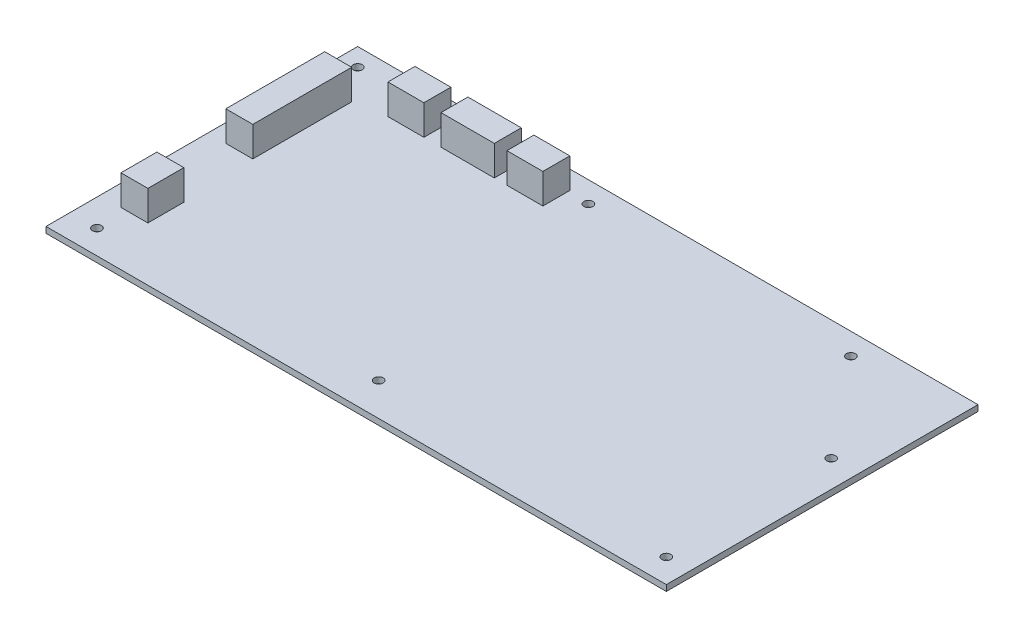
SolidWorks part; units mm, degrees
material "Cuivre"
ref_plane "Plan de face" through (0, 0, 0) normal (0, 0, 1) x (1, 0, 0)
ref_plane "Plan de dessus" through (0, 0, 0) normal (0, 1, 0) x (1, 0, 0)
ref_plane "Plan de droite" through (0, 0, 0) normal (1, 0, 0) x (0, 0, -1)
sketch "Esquisse1" plane through (0, 0, 0) normal (0, 1, 0) x (1, 0, 0)
  line L1 (-103.5, -52) -> (103.5, -52)
  line L2 (-103.5, -52) -> (-103.5, 52)
  line L3 (-103.5, 52) -> (103.5, 52)
  line L4 (103.5, -52) -> (103.5, 52)
  line L5 (-103.5, -52) -> (103.5, 52) construction
  line L6 (-103.5, 52) -> (103.5, -52) construction
  point P0 (0, 0)
  dimension "D1" = 207
  dimension "D2" = 104
extrude "Boss.-Extru.1" add sketch "Esquisse1" along normal blind 2
sketch "Esquisse3" plane through (0, 2, 0) normal (0, 1, 0) x (1, 0, 0)
  line L0 (103.5, 52) -> (-103.5, 52) construction
  line L1 (-103.5, 52) -> (-103.5, -52) construction
  circle A0 centre (-97.5, 46) radius 1.5
  circle A1 centre (-19.5, 45) radius 1.5
  circle A2 centre (68.3, 44.8) radius 1.5
  circle A3 centre (94.5, 12) radius 1.5
  circle A4 centre (95.5, -44) radius 1.5
  circle A5 centre (-3.5, -41) radius 1.5
  circle A6 centre (-94.5, -44) radius 1.5
  point P20 (-93.1032, -80.1049)
  dimension "D1" = 3
  dimension "D16" = 3
  dimension "D17" = 3
  dimension "D18" = 3
  dimension "D19" = 3
  dimension "D20" = 3
  dimension "D21" = 3
  dimension "D2" = 6
  dimension "D3" = 6
  dimension "D4" = 96
  dimension "D5" = 9
  dimension "D6" = 100
  dimension "D7" = 93
  dimension "D8" = 199
  dimension "D9" = 96
  dimension "D10" = 40
  dimension "D11" = 198
  dimension "D12" = 171.8
  dimension "D13" = 7.2
  dimension "D14" = 7
  dimension "D15" = 84
extrude "Enlèv. mat.-Extru.1" cut sketch "Esquisse3" against normal through all
sketch "Esquisse4" plane through (0, 2, 0) normal (0, 1, 0) x (1, 0, 0)
  line L0 (-103.5, 52) -> (-103.5, -52) construction
  line L1 (-97.5, 35) -> (-88.5, 35)
  line L2 (-97.5, 35) -> (-97.5, 2)
  line L3 (-97.5, 2) -> (-88.5, 2)
  line L4 (-88.5, 35) -> (-88.5, 2)
  line L5 (-96.5, -22) -> (-87.5, -22)
  line L6 (-96.5, -22) -> (-96.5, -34)
  line L7 (-96.5, -34) -> (-87.5, -34)
  line L8 (-87.5, -22) -> (-87.5, -34)
  line L9 (-78.2, 45.8) -> (-66.2, 45.8)
  line L10 (-78.2, 45.8) -> (-78.2, 36.8)
  line L11 (-78.2, 36.8) -> (-66.2, 36.8)
  line L12 (-66.2, 45.8) -> (-66.2, 36.8)
  line L13 (-60.5, 45.8) -> (-42.7, 45.8)
  line L14 (-60.5, 45.8) -> (-60.5, 36.8)
  line L15 (-60.5, 36.8) -> (-42.7, 36.8)
  line L16 (-42.7, 45.8) -> (-42.7, 36.8)
  line L17 (-38.5, 45.8) -> (-26.5, 45.8)
  line L18 (-38.5, 45.8) -> (-38.5, 36.8)
  line L19 (-38.5, 36.8) -> (-26.5, 36.8)
  line L20 (-26.5, 45.8) -> (-26.5, 36.8)
  line L21 (103.5, 52) -> (-103.5, 52) construction
  dimension "D1" = 9
  dimension "D2" = 33
  dimension "D3" = 9
  dimension "D4" = 12
  dimension "D5" = 12
  dimension "D6" = 9
  dimension "D7" = 12
  dimension "D8" = 9
  dimension "D9" = 9
  dimension "D10" = 17.8
  dimension "D11" = 7
  dimension "D12" = 74
  dimension "D13" = 6
  dimension "D14" = 17
  dimension "D15" = 25.3
  dimension "D16" = 6.2
  dimension "D17" = 43
  dimension "D18" = 65
extrude "Boss.-Extru.2" add sketch "Esquisse4" along normal blind 10
